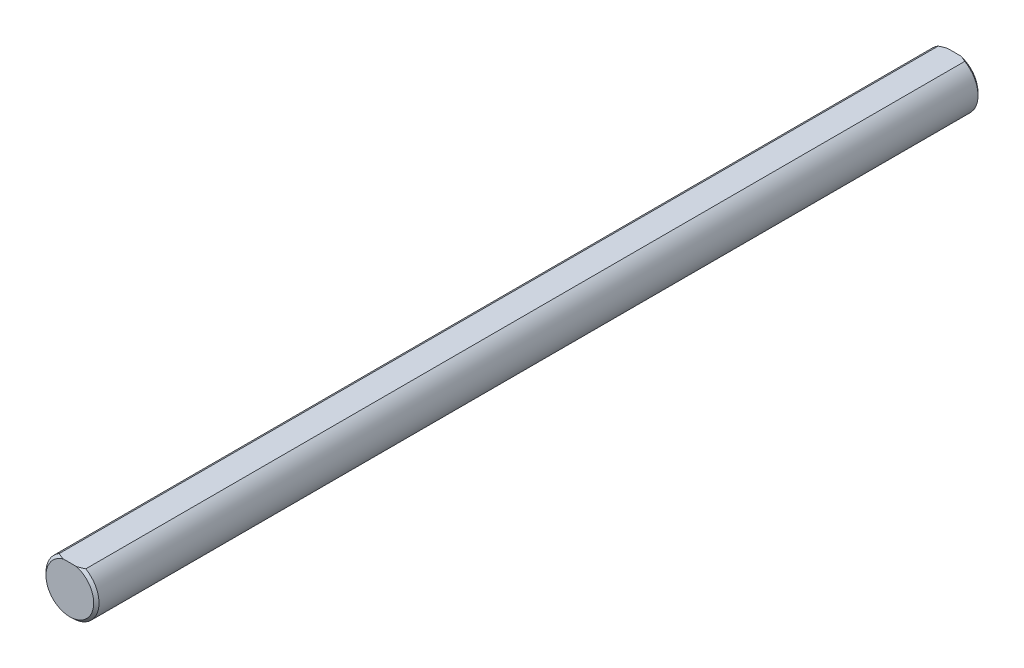
SolidWorks part; units mm, degrees
ref_plane "Front Plane" through (0, 0, 0) normal (0, 0, 1) x (1, 0, 0)
ref_plane "Top Plane" through (0, 0, 0) normal (0, 1, 0) x (1, 0, 0)
ref_plane "Right Plane" through (0, 0, 0) normal (1, 0, 0) x (0, 0, -1)
sketch "Sketch1" plane through (0, 0, 0) normal (0, 0, 1) x (1, 0, 0)
  line L0 (3, 5.1962) -> (-3, 5.1962) construction
  line L1 (0, 5.1962) -> (0, 0) construction
  line L2 (0, 0) -> (0, -6) construction
  circle A1 centre (0, 0) radius 6 construction
  dimension "Diameter" = 12
  dimension "Flat Width" = 6
  dimension "D1" = 11.1962
sketch "Sketch2" plane through (0, 0, 0) normal (1, 0, 0) x (0, 0, -1)
  line L0 (-100, 6) -> (100, 6) construction
  line L1 (0, 6) -> (0, -6) construction
  line L2 (0, 6) -> (0, -6) construction
  line L3 (-100, 6) -> (-100, 0) construction
  line L4 (-100, 0) -> (0, 0) construction
  line L6 (-100, 5.4) -> (-99.4, 6) construction
  point P2 (0, 6)
  point P3 (76, 6)
  point P4 (-76, 6)
  dimension "Length/ D-Profile Length" = 200
  dimension "D2" = 24
  dimension "D1" = 24
  dimension "Chamfer Typ." = 45
  dimension "D4" = 0.6
sketch "Sketch3" plane through (0, 0, 0) normal (0, 0, 1) x (1, 0, 0)
  circle A1 centre (0, 0) radius 6 construction
  circle A3 centre (0, 0) radius 6
extrude "Boss-Extrude2" add sketch "Sketch3" along normal up to vertex (100 mm away) and the other way up to vertex (100 mm away) up to point (0, 6, 100) other way up to point (0, 6, -100)
sketch "Sketch10" plane through (0, 0, 0) normal (0, 0, 1) x (1, 0, 0)
  line L0 (-3, 5.1962) -> (3, 5.1962)
  line L1 (0, 0) -> (0, 6) construction
  circle A0 centre (0, 0) radius 6 construction
  circle A1 centre (0, 0) radius 6 construction
  arc A2 (-3, 5.1962) -> (3, 5.1962) centre (0, 0) cw
extrude "Cut-Extrude5" cut sketch "Sketch10" against normal through all both and the other way through all
chamfer "Chamfer1" distance 0.6 angle 45 4 edges at (0, -6, 100) (0, -6, -100) (0, 5.1962, -100) (0, 5.1962, 100)
equation "\"D1@Chamfer1\"= \"Diameter@Sketch1\" / 20"
equation "\"D1@Sketch2\"=\"Diameter@Sketch1\"*2"
equation "\"D2@Sketch2\"=\"D1@Sketch2\""
equation "\"D4@Sketch2\"=\"Diameter@Sketch1\" / 20"
